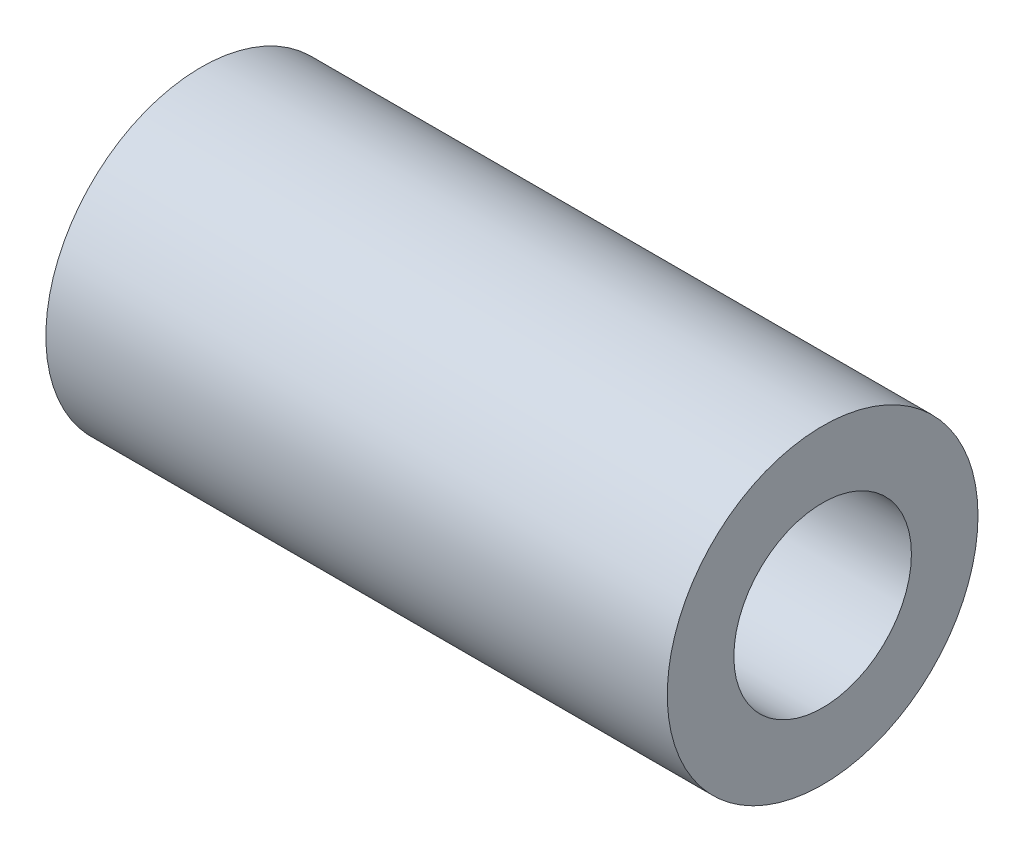
SolidWorks part; units mm, degrees
ref_plane "Alzado" through (0, 0, 0) normal (0, 0, 1) x (1, 0, 0)
ref_plane "Planta" through (0, 0, 0) normal (0, 1, 0) x (1, 0, 0)
ref_plane "Vista lateral" through (0, 0, 0) normal (1, 0, 0) x (0, 0, -1)
sketch "Croquis1" plane through (0, 0, 0) normal (1, 0, 0) x (0, 0, -1)
  circle A0 centre (0, 0) radius 7
  circle A1 centre (0, 0) radius 4
  dimension "D1" = 14
  dimension "D2" = 8
extrude "Saliente-Extruir1" add sketch "Croquis1" along normal mid plane 28
